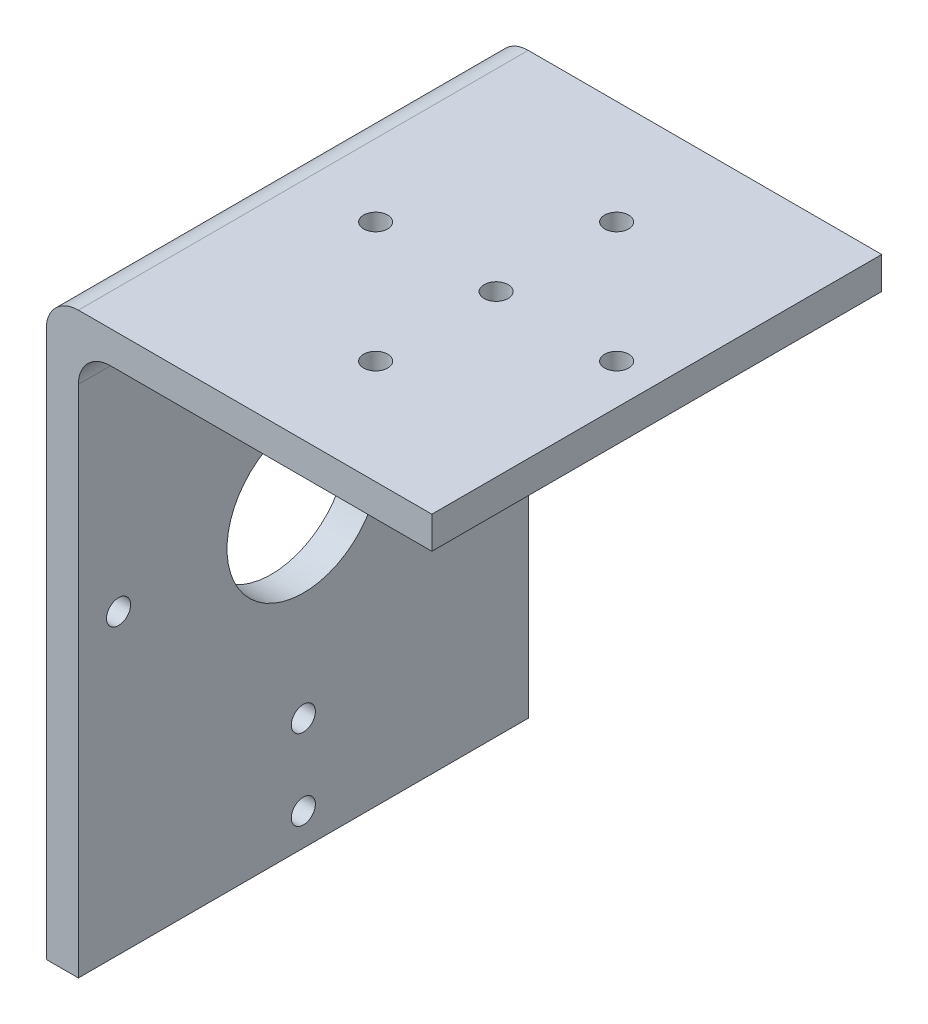
SolidWorks part; units mm, degrees
material "Acrylic (Medium-high impact)"
ref_plane "Front Plane" through (0, 0, 0) normal (0, 0, 1) x (1, 0, 0)
ref_plane "Top Plane" through (0, 0, 0) normal (0, 1, 0) x (1, 0, 0)
ref_plane "Right Plane" through (0, 0, 0) normal (1, 0, 0) x (0, 0, -1)
sketch "Sketch2" plane through (0, 0, 0) normal (0, 0, 1) x (1, 0, 0)
  line L0 (-30.3062, -59.3983) -> (-26.3062, -59.3983)
  line L1 (-26.3062, -59.3983) -> (-26.3062, 8.6017)
  line L2 (-26.3062, 8.6017) -> (17.6938, 8.6017)
  line L3 (17.6938, 8.6017) -> (17.6938, 12.6017)
  line L4 (17.6938, 12.6017) -> (-30.3062, 12.6017)
  line L5 (-30.3062, 12.6017) -> (-30.3062, -59.3983)
extrude "Boss-Extrude1" add sketch "Sketch2" along normal blind 28 and the other way blind 28
sketch "Sketch3" plane through (-26.3062, 0, 0) normal (1, 0, 0) x (0, 0, -1)
  line L0 (28, 12.6017) -> (-28, 12.6017) construction
  line L1 (-28, -59.3983) -> (-28, 8.6017) construction
  circle A0 centre (0, -22.3983) radius 9.5
  circle A1 centre (0, 0.6017) radius 1.5
  circle A2 centre (23, -22.3983) radius 1.5
  circle A3 centre (0, -22.3983) radius 9.5
  circle A4 centre (0, -45.3983) radius 1.5
  circle A5 centre (0, -22.3983) radius 9.5
  circle A6 centre (-23, -22.3983) radius 1.5
  circle A7 centre (0, -22.3983) radius 9.5
  circle A8 centre (0, -55.3983) radius 1.5
  point P19 (0, -22.3983)
  dimension "D1" = 19
  dimension "D2" = 28
  dimension "D4" = 28
  dimension "D6" = 4
  dimension "D8" = 3
  dimension "D7" = 10
  dimension "D3" = 35
  dimension "D5" = 23
extrude "Cut-Extrude1" cut sketch "Sketch3" against normal blind 4 contours A0 | A6 | A1 | A2 | A4 | A8
fillet "Fillet2" radius 4 2 edges at (-26.3062, 8.6017, 0) (-30.3062, 12.6017, 0)
sketch "Sketch4" plane through (0, 8.6017, 0) normal (0, -1, 0) x (1, 0, 0)
  line L0 (-22.3062, -28) -> (17.6938, -28) construction
  line L1 (-22.3062, 28) -> (-22.3062, -28) construction
  line L2 (-2.3062, 0) -> (-17.3062, 0) construction
  circle A0 centre (-2.3062, 0) radius 1.5
  circle A1 centre (-17.3062, 0) radius 1.5
  circle A2 centre (-2.3062, 15) radius 1.5
  circle A3 centre (12.6938, 0) radius 1.5
  circle A4 centre (-2.3062, -15) radius 1.5
  dimension "D1" = 28
  dimension "D3" = 15
  dimension "D6" = 4
  dimension "D7" = 13
  dimension "D2" = 20
  dimension "D4" = 28
  dimension "D5" = 15
extrude "Cut-Extrude2" cut sketch "Sketch4" against normal blind 4
